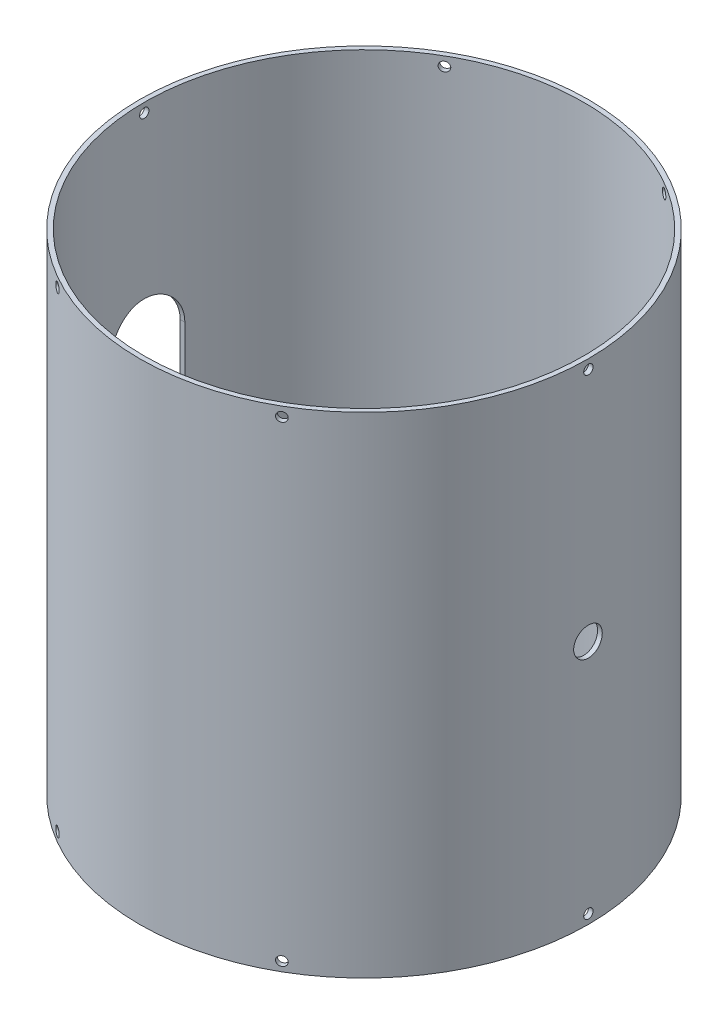
SolidWorks part; units mm, degrees
material "6061-T6 (SS)"
ref_plane "Front Plane" through (0, 0, 0) normal (0, 0, 1) x (1, 0, 0)
ref_plane "Top Plane" through (0, 0, 0) normal (0, 1, 0) x (1, 0, 0)
ref_plane "Right Plane" through (0, 0, 0) normal (1, 0, 0) x (0, 0, -1)
sketch "Sketch1" plane through (0, 0, 0) normal (0, 1, 0) x (1, 0, 0)
  circle A0 centre (0, 0) radius 149.225
  circle A1 centre (0, 0) radius 152.4
  dimension "D1" = 304.8
  dimension "D2" = 298.45
extrude "Boss-Extrude1" add sketch "Sketch1" along normal blind 332.74
ref_plane "Plane1" through (-152.4, 0, 0) normal (-1, 0, 0) x (0, 0, 1)
sketch "Sketch2" plane through (-152.4, 0, 0) normal (-1, 0, 0) x (0, 0, 1)
  line L0 (0, 191.77) -> (0, 140.97) construction
  line L1 (-224.71, 166.37) -> (224.71, 166.37) construction
  line L2 (25.4, 191.77) -> (25.4, 140.97)
  line L3 (-25.4, 191.77) -> (-25.4, 140.97)
  arc A0 (25.4, 191.77) -> (-25.4, 191.77) centre (0, 191.77) ccw
  arc A1 (-25.4, 140.97) -> (25.4, 140.97) centre (0, 140.97) ccw
  point P2 (0, 166.37)
  point P11 (0, 217.17)
  point P12 (0, 115.57)
  dimension "D3" = 166.37
  dimension "D1" = 101.6
  dimension "D2" = 50.8
extrude "Cut-Extrude1" cut sketch "Sketch2" against normal blind 190.5 contours L3 A1 L2 A0
ref_plane "Plane2" through (152.4, 0, 0) normal (1, 0, 0) x (0, 0, -1)
sketch "Sketch3" plane through (152.4, 0, 0) normal (1, 0, 0) x (0, 0, -1)
  line L0 (152.4, 332.74) -> (-152.4, 332.74) construction
  circle A1 centre (0, 166.37) radius 9.7155
  dimension "D1" = 19.431
  dimension "D2" = 166.37
extrude "Cut-Extrude2" cut sketch "Sketch3" against normal blind 190.5
ref_plane "Plane3" through (152.4, 0, 0) normal (1, 0, 0) x (0, 0, -1)
sketch "Sketch4" plane through (152.4, 0, 0) normal (1, 0, 0) x (0, 0, -1)
  line L0 (-205.001, 166.37) -> (213.6941, 166.37) construction
  line L1 (-152.4, 0) -> (152.4, 0) construction
  line L3 (149.225, 332.74) -> (-149.225, 332.74) construction
  circle A0 centre (0, 6.35) radius 3.175
  circle A1 centre (0, 326.39) radius 3.175
  dimension "D3" = 166.37
  dimension "D1" = 6.35
  dimension "D2" = 6.35
extrude "Cut-Extrude3" cut sketch "Sketch4" against normal through all both and the other way through all
pattern_circular "CirPattern1" count 3 over 360 about axis through (0, 332.74, 0) along (0, -1, 0) of "Cut-Extrude3"
equation "\"OD\"= 12'rocket body outer diameter"
equation "\"D1@Sketch1\"=\"OD\""
equation "\"airframe_thickness\"= 0.125in'thickness of airframe"
equation "\"intertank_height\"= 7.5 + 5.6in'height required for bulkheads, plumbing bend angles plus 1.5 FOS"
equation "\"D2@Sketch1\"=\"OD\" - 2*\"airframe_thickness\""
equation "\"D1@Boss-Extrude1\"=\"intertank_height\""
equation "\"OXFUEL_PORT\"=2"
equation "\"D3@Sketch2\"=\"intertank_height\"/2"
equation "\"PRESS_PORT\"=0.765"
equation "\"D1@Sketch3\"=\"PRESS_PORT\""
equation "\"D2@Sketch3\"=\"intertank_height\"/2"
equation "\"D1@Sketch2\"=2*\"OXFUEL_PORT\""
equation "\"D2@Sketch2\"=\"OXFUEL_PORT\""
equation "\"AIRFRAME_BOLT\"=0.25"
equation "\"D1@Sketch4\"=\"AIRFRAME_BOLT\""
equation "\"D2@Sketch4\"=\"AIRFRAME_BOLT\""
equation "\"D3@Sketch4\"=\"intertank_height\"/2"
